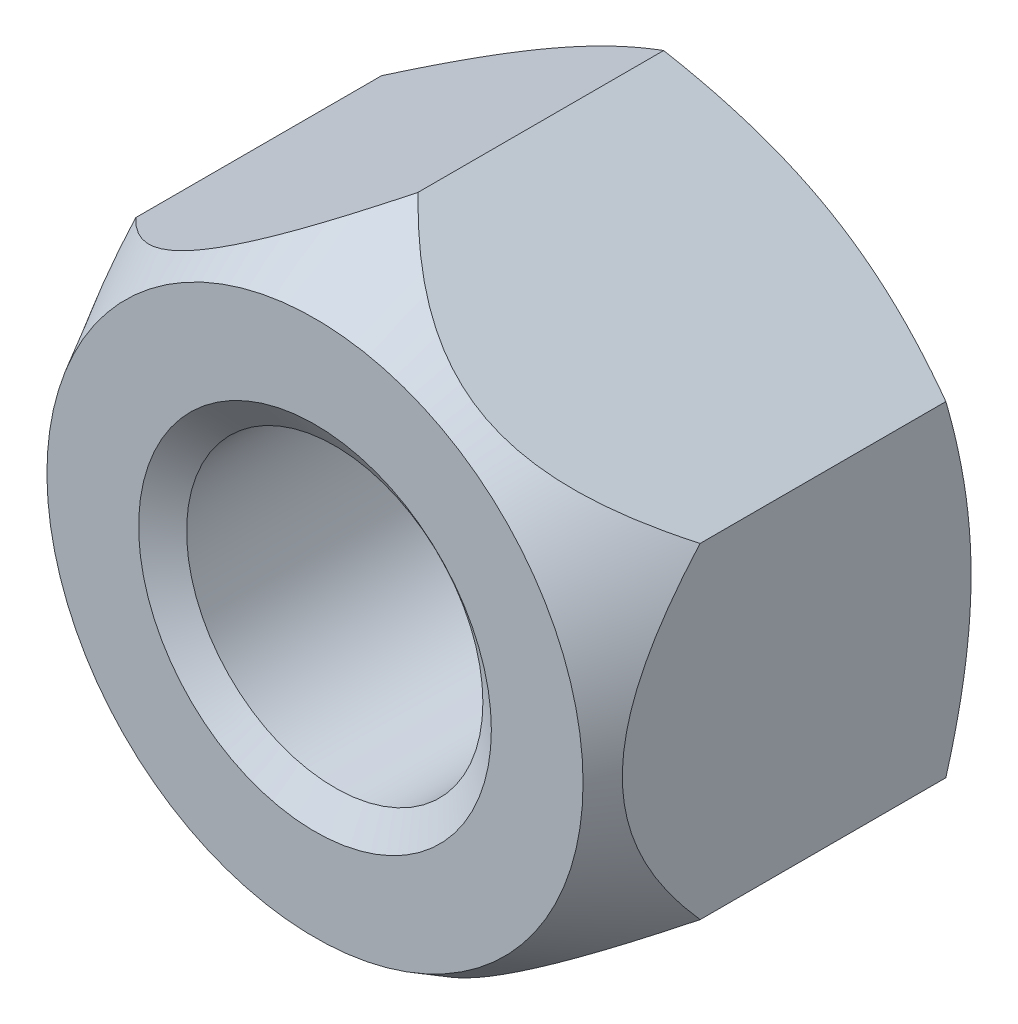
SolidWorks part; units mm, degrees
extrude "BaseNut" add sketch "BaseNutSke" against normal blind 5.3
sketch "BaseNutSke" plane through (0, 0, 0) normal (0, 0, 1) x (1, 0, 0)
  line L6 (4, 2.3094) -> (4, -2.3094)
  line L7 (-4, 2.3094) -> (-4, -2.3094)
  line L8 (4, 2.3094) -> (0, 4.6188)
  line L9 (0, 4.6188) -> (-4, 2.3094)
  line L10 (-4, -2.3094) -> (0, -4.6188)
  line L11 (0, -4.6188) -> (4, -2.3094)
  circle A0 centre (0, 0) radius 2.1
  dimension "Tap_drill" = 4.2
  dimension "Width_flats" = 8
  dimension "D2" = 4
  dimension "D3" = 4
  dimension "D1" = 120
  dimension "D4" = 4
pattern_linear "ThdSchPat" [suppressed]
revolve "ThreadSchematic" [suppressed] cut sketch "ThdSchSke" angle 360 about L6
sketch "ThdSchSke" plane through (0, 0, 0) normal (0, 1, 0) x (1, 0, 0)
  line L0 (-2.5, 0.0254) -> (-2.1, 0.3055)
  line L1 (-2.1, 0.3055) -> (-1.05, 0.3055)
  line L2 (-1.05, 0.3055) -> (-1.05, -0.2547)
  line L3 (-1.05, -0.2547) -> (-2.1, -0.2547)
  line L4 (-2.1, -0.2547) -> (-2.5, 0.0254)
  line L5 (-3.175, 0.8) -> (3.175, 0.8) construction
  line L6 (0, 0.8) -> (0, -2.9874) construction
  line L7 (0, 4.9945) -> (0, 0.2801) construction
  dimension "SideAngle" = 55
  dimension "Advance" = 0.8
  dimension "D1" = 0.0254
  dimension "Thread_major" = 5
ref_plane "Plane1" through (0, 0, 0) normal (0, 0, 1) x (1, 0, 0)
ref_plane "Plane2" through (0, 0, 0) normal (0, 1, 0) x (1, 0, 0)
ref_plane "Plane3" through (0, 0, 0) normal (1, 0, 0) x (0, 0, -1)
sketch "Sketch3" plane through (0, 0, 0) normal (1, 0, 0) x (0, 0, -1)
  line L0 (5.3, 4) -> (4.9427, 4.6188)
  line L1 (4.9427, 4.6188) -> (4.9427, 14.6188)
  line L2 (4.9427, 14.6188) -> (15.3, 14.6188)
  line L3 (15.3, 14.6188) -> (15.3, 4)
  line L4 (15.3, 4) -> (5.3, 4)
  line L5 (5.3, 2.3094) -> (5.3, 4.6188) construction
  line L6 (5.3, 4.6188) -> (0, 4.6188) construction
  line L7 (0, 0) -> (38.6776, 0) construction
  line L8 (5.3, 0) -> (0, 0) construction
  line L10 (1.46, 14.6188) -> (-10, 14.6188)
  line L11 (-10, 14.6188) -> (-10, 3.8)
  line L12 (-10, 3.8) -> (0, 3.8)
  line L13 (0, 3.8) -> (1.46, 4.6188)
  line L14 (1.46, 4.6188) -> (1.46, 14.6188)
  line L15 (5.3, -2.1) -> (5.3, 2.1) construction
  line L16 (5.3, 4.6188) -> (0, 4.6188) construction
  line L17 (0, 2.3094) -> (0, -2.3094) construction
  dimension "D1" = 4
  dimension "D4" = 10
  dimension "D3" = 10
  dimension "D2" = 30
  dimension "D6" = 10
  dimension "D8" = 3.8
  dimension "D7" = 10
revolve "Double-Chamfer" cut sketch "Sketch3" angle 360 about L7
sketch "Sketch5" plane through (0, 0, 0) normal (1, 0, 0) x (0, 0, -1)
  line L0 (5.2746, 2.5) -> (4.9665, 2.06)
  line L1 (5.3254, 2.5) -> (5.2746, 2.5)
  line L2 (5.3254, 2.5) -> (5.3254, 2.06)
  line L3 (5.3254, 2.06) -> (4.9665, 2.06)
  line L6 (-0.0508, 2.5) -> (0, 2.5)
  line L7 (0, 2.5) -> (0.3081, 2.06)
  line L9 (0.3081, 2.06) -> (-0.0508, 2.06)
  line L10 (-0.0508, 2.06) -> (-0.0508, 2.5)
  line L11 (25.0375, 0) -> (38.388, 0) construction
  line L12 (5.3, 0) -> (0, 0) construction
  dimension "D1" = 35
  dimension "D2" = 0.0508
  dimension "ThreadMajor" = 2.5
  dimension "Offset1" = 5.3254
revolve "EndChamfer" cut sketch "Sketch5" angle 360 about L11
equation "\"D2@BaseNutSke\" = \"Width_flats@BaseNutSke\" / 2"
equation "\"D3@BaseNutSke\" = \"Width_flats@BaseNutSke\" / 2"
equation "\"D1@Sketch3\" = \"Width_flats@BaseNutSke\" /2"
equation "\"D4@BaseNutSke\" = \"D3@BaseNutSke\""
equation "\"Thread_major@ThdSchSke\" = \"Thread_major@ThreadCosmetic\""
equation "\"Tap_Drill@ThdSchSke\" = \"Tap_drill@BaseNutSke\""
equation "\"OverCut@ThdSchSke\" = \"Tap_Drill@ThdSchSke\" * 0.5"
equation "\"Num_threads@ThdSchPat\" = int(  ( \"Thickness@BaseNut\" - 0.0508 ) / \"Advance@ThdSchSke\" + 0.999 )  + 1"
equation "\"Advance@ThdSchPat\" = ( \"Thickness@BaseNut\" - 0.0508 ) /  (\"Num_threads@ThdSchPat\" - 1) 'relax it"
equation "' \"Num_threads@ThdSchPat\" = \"Num_threads@ThdSchPat\" - sgn( \"Num_threads@ThdSchPat\" - 1) '---chamfered tips only---"
equation "\"ThreadMajor@Sketch5\" = \"Thread_major@ThreadCosmetic\" * 0.5"
equation "\"ChamferDepth@Sketch5\" = (\"Thread_major@ThreadCosmetic\" - \"Tap_drill@BaseNutSke\") * 0.55"
equation "\"Offset1@Sketch5\" = \"Thickness@BaseNut\" + 0.0254"
equation "\"Offset2@Sketch5\" = \"Offset1@Sketch5\" + 0.0508"
equation "\"D8@Sketch3\" = 0.95 *\"D1@Sketch3\""
